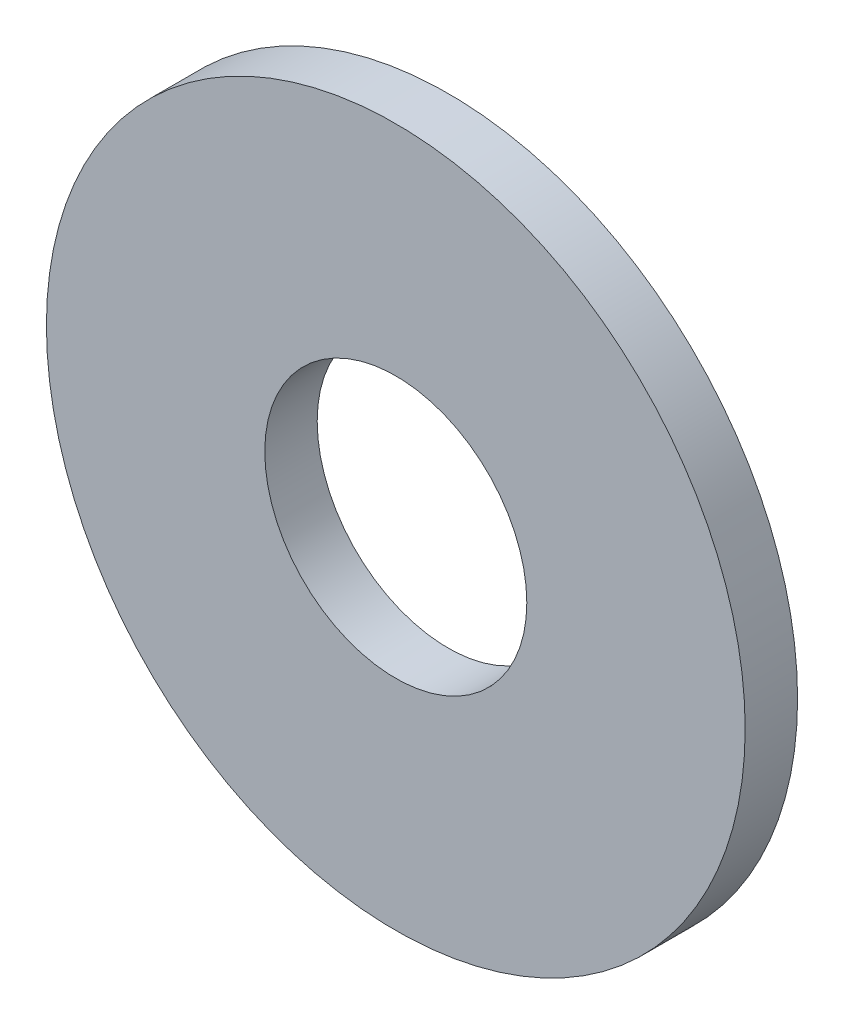
SolidWorks part; units mm, degrees
ref_plane "Front Plane" through (0, 0, 0) normal (0, 0, 1) x (1, 0, 0)
ref_plane "Top Plane" through (0, 0, 0) normal (0, 1, 0) x (1, 0, 0)
ref_plane "Right Plane" through (0, 0, 0) normal (1, 0, 0) x (0, 0, -1)
sketch "Sketch1" plane through (0, 0, 0) normal (0, 0, 1) x (1, 0, 0)
  circle A0 centre (0, 0) radius 1.5
  circle A1 centre (0, 0) radius 4
  dimension "D1" = 3
  dimension "D2" = 8
extrude "Boss-Extrude1" add sketch "Sketch1" along normal blind 0.6
